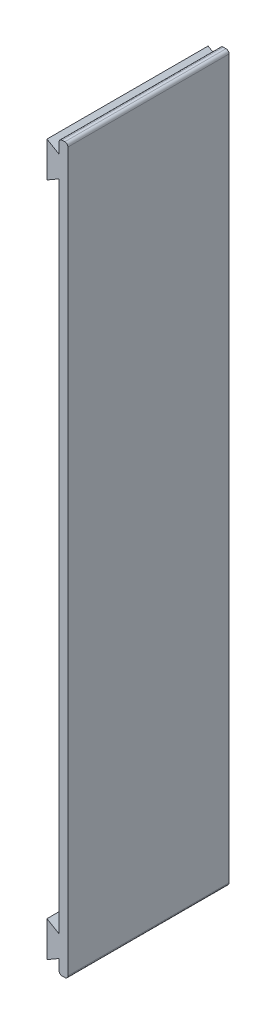
SolidWorks part; units mm, degrees
ref_plane "Front Plane" through (0, 0, 0) normal (0, 0, 1) x (1, 0, 0)
ref_plane "Top Plane" through (0, 0, 0) normal (0, 1, 0) x (1, 0, 0)
ref_plane "Right Plane" through (0, 0, 0) normal (1, 0, 0) x (0, 0, -1)
sketch "Sketch2" plane through (0, 0, 0) normal (0, 0, 1) x (1, 0, 0)
  line L0 (0, 0) -> (0, -4.48)
  line L2 (2.9, -7.4588) -> (2.9, 0)
  line L3 (2.9, 0) -> (0, 0)
  line L4 (0, 0) -> (0, -4.48) construction
  line L5 (0, -19) -> (0, -11.52) construction
  line L6 (0, -4.48) -> (4.0097, -2.165) construction
  line L10 (0, -19) -> (0, -219)
  line L11 (0, -119) -> (59.9435, -119) construction
  line L12 (2.9, -238) -> (0, -238)
  line L13 (2.9, -230.5412) -> (2.9, -238)
  line L15 (0, -238) -> (0, -233.52)
  line L19 (0, -226.48) -> (0, -219)
  line L20 (0, -11.52) -> (0, -19)
  line L21 (2.9, -230.5412) -> (2.9, -7.4588)
  line L22 (0, -4.48) -> (-3.9924, -2.175)
  line L23 (0, -11.52) -> (-3.9924, -13.825)
  line L24 (-3.9924, -2.175) -> (-3.9924, -13.825)
  line L25 (0, -233.52) -> (-3.9924, -235.825)
  line L26 (-3.9924, -235.825) -> (-3.9924, -224.175)
  line L27 (0, -226.48) -> (-3.9924, -224.175)
  dimension "D1" = 19
  dimension "D2" = 11.9
  dimension "D3" = 4.48
  dimension "D4" = 7.48
  dimension "D5" = 60
  dimension "D6" = 11.65
  dimension "D8" = 200
  dimension "D9" = 2.9
  dimension "D10" = 60
  dimension "D11" = 60
  dimension "D12" = 11.65
  dimension "D13" = 60
extrude "Boss-Extrude1" add sketch "Sketch2" along normal blind 53
sketch "Sketch3" plane through (0, 0, 0) normal (1, 0, 0) x (0, 0, -1)
  line L0 (0, -119) -> (0, -58.5)
  line L3 (0, -11.52) -> (0, -226.48) construction
  line L4 (0, -119) -> (0, -179.5)
  line L5 (0, -58.5) -> (-2.8, -58.5)
  line L6 (-2.8, -58.5) -> (-2.8, -179.5)
  line L7 (-2.8, -179.5) -> (0, -179.5)
  point P5 (-5.9, -144.9585)
  point P6 (0, -158.9397)
  dimension "D1" = 121
  dimension "D2" = 2.8
  dimension "D3" = 60.5
extrude "Boss-Extrude2" add sketch "Sketch3" against normal blind 8
sketch "Sketch4" plane through (2.9, 0, 0) normal (1, 0, 0) x (0, 0, -1)
  line L2 (-50, -238) -> (-50, 0)
  line L3 (-50, -235) -> (-50, -5)
  line L8 (-53, -235) -> (0, -235)
  line L9 (-50, -235) -> (-5, -235)
  line L11 (-5, -238) -> (-5, 0)
  line L12 (-5, -235) -> (-5, -5)
  line L22 (-5, -5) -> (-5, -238)
  line L23 (-53, -5) -> (-5, -5)
  line L24 (-5, -5) -> (-5, -235)
  line L25 (-50, -5) -> (-5, -5)
  dimension "D1" = 3
  dimension "D2" = 3
  dimension "D3" = 5
  dimension "D4" = 5
extrude "Cut-Extrude2" [suppressed] cut sketch "Sketch4" against normal blind 1 contours L25 L3 L9 L12
fillet "Fillet2" radius 1 4 edges at (0, -238, 26.5) (2.9, -238, 26.5) (2.9, 0, 26.5) (0, 0, 26.5)
fillet "Fillet3" radius 1 8 edges at (-8, -179.5, 1.4) (-4, -179.5, 0) (-4, -179.5, 2.8) (-8, -58.5, 1.4) (-4, -58.5, 0) (-4, -58.5, 2.8) (-8, -119, 0) (-8, -119, 2.8)
